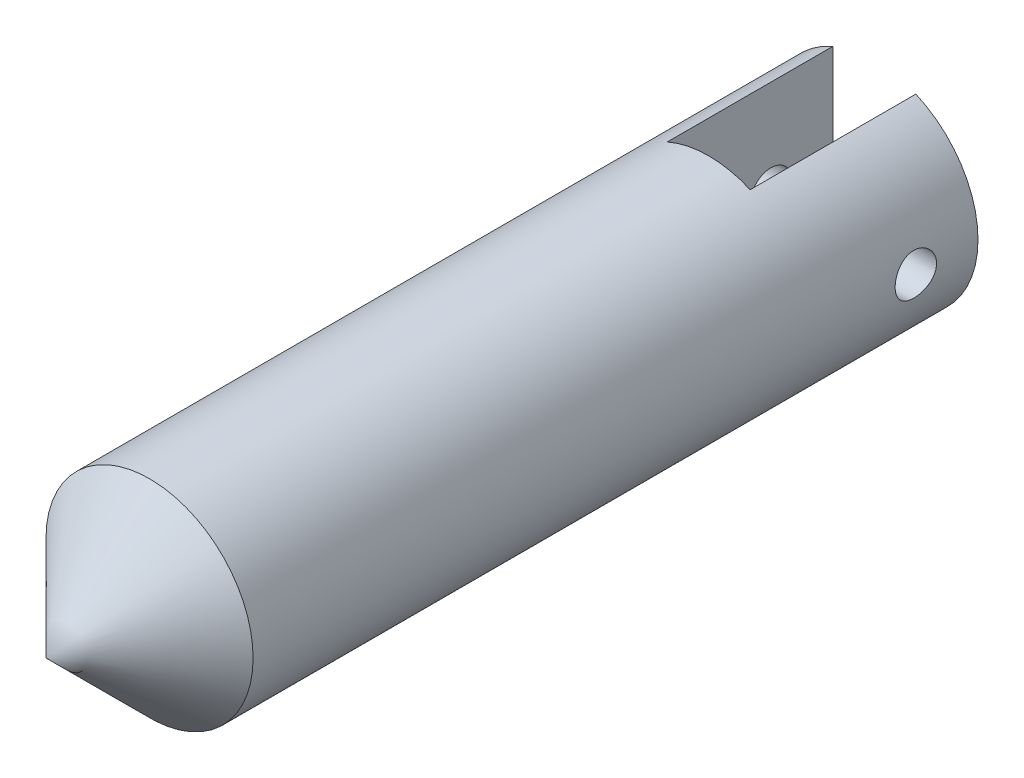
SolidWorks part; units mm, degrees
ref_plane "Front Plane" through (0, 0, 0) normal (0, 0, 1) x (1, 0, 0)
ref_plane "Top Plane" through (0, 0, 0) normal (0, 1, 0) x (1, 0, 0)
ref_plane "Right Plane" through (0, 0, 0) normal (1, 0, 0) x (0, 0, -1)
sketch "Sketch2" plane through (0, 0, 0) normal (0, 0, 1) x (1, 0, 0)
  circle A0 centre (0, 0) radius 6.35
  dimension "D1" = 12.7
extrude "Boss-Extrude1" add sketch "Sketch2" along normal blind 44.45
sketch "Sketch3" plane through (0, 0, 0) normal (1, 0, 0) x (0, 0, -1)
  line L0 (-50.8, 0) -> (-44.45, 6.35)
  line L1 (-50.8, 0) -> (-44.45, 0)
  line L2 (-44.45, 6.35) -> (-44.45, -6.35) construction
  line L3 (-44.45, 0) -> (-44.45, 6.35)
  dimension "D1" = 6.35
revolve "Revolve1" add sketch "Sketch3" angle 360 about L1
sketch "Sketch4" plane through (0, 0, 0) normal (0, 0, -1) x (-1, 0, 0)
  line L1 (-2.54, -6.35) -> (2.54, -6.35)
  line L2 (-2.54, -6.35) -> (-2.54, 6.35)
  line L3 (-2.54, 6.35) -> (2.54, 6.35)
  line L4 (2.54, -6.35) -> (2.54, 6.35)
  line L5 (-2.54, -6.35) -> (2.54, 6.35) construction
  line L6 (-2.54, 6.35) -> (2.54, -6.35) construction
  point P0 (0, 0)
  dimension "D1" = 12.7
  dimension "D2" = 5.08
extrude "Cut-Extrude1" cut sketch "Sketch4" against normal blind 10.16
sketch "Sketch5" plane through (2.54, 0, 0) normal (-1, 0, 0) x (0, 0, 1)
  circle A0 centre (3.81, 0) radius 1.27
  dimension "D1" = 2.54
  dimension "D2" = 3.81
extrude "Cut-Extrude2" cut sketch "Sketch5" against normal through all and the other way through all
